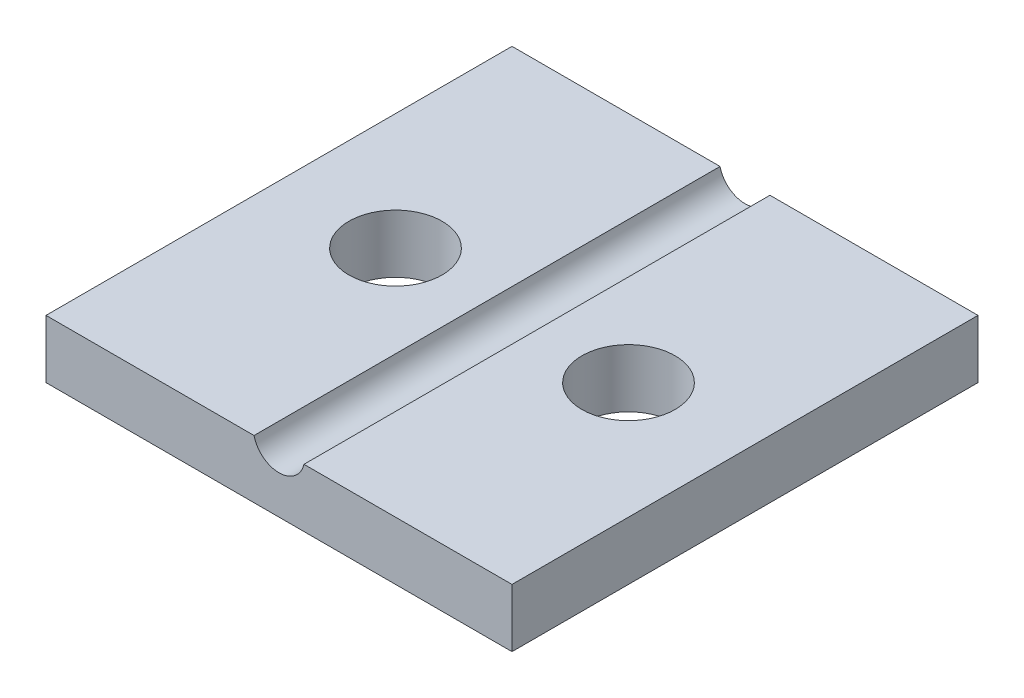
SolidWorks part; units mm, degrees
ref_plane "Front Plane" through (0, 0, 0) normal (0, 0, 1) x (1, 0, 0)
ref_plane "Top Plane" through (0, 0, 0) normal (0, 1, 0) x (1, 0, 0)
ref_plane "Right Plane" through (0, 0, 0) normal (1, 0, 0) x (0, 0, -1)
sketch "Sketch1" plane through (0, 0, 0) normal (0, 1, 0) x (1, 0, 0)
  line L1 (-60.7547, 52.0755) -> (-40.7547, 52.0755)
  line L2 (-60.7547, 52.0755) -> (-60.7547, 32.0755)
  line L3 (-60.7547, 32.0755) -> (-40.7547, 32.0755)
  line L4 (-40.7547, 52.0755) -> (-40.7547, 32.0755)
  dimension "D1" = 20
  dimension "D2" = 20
extrude "Boss-Extrude1" add sketch "Sketch1" along normal blind 2.5
sketch "Sketch2" plane through (0, 0, -32.0755) normal (0, 0, 1) x (1, 0, 0)
  line L0 (-60.7547, 2.5) -> (-40.7547, 2.5) construction
  line L1 (-50.7547, 6.7696) -> (-50.7547, 3.4135) construction
  circle A0 centre (-50.7547, 2.75) radius 1.1
  point P6 (-50.7547, 2.5)
  dimension "D2" = 2.2
  dimension "D1" = 0.25
extrude "Cut-Extrude1" cut sketch "Sketch2" against normal through all contours A0
sketch "Sketch3" plane through (0, 2.5, 0) normal (0, 1, 0) x (1, 0, 0)
  line L0 (-55.7547, 42.0755) -> (-45.7547, 42.0755) construction
  line L3 (-60.7547, 52.0755) -> (-40.7547, 32.0755) construction
  line L4 (-40.7547, 52.0755) -> (-60.7547, 32.0755) construction
  circle A0 centre (-55.7547, 42.0755) radius 2
  circle A1 centre (-45.7547, 42.0755) radius 2
  point P2 (-50.7547, 42.0755)
  dimension "D2" = 4
  dimension "D1" = 10
extrude "Cut-Extrude2" cut sketch "Sketch3" against normal through all
